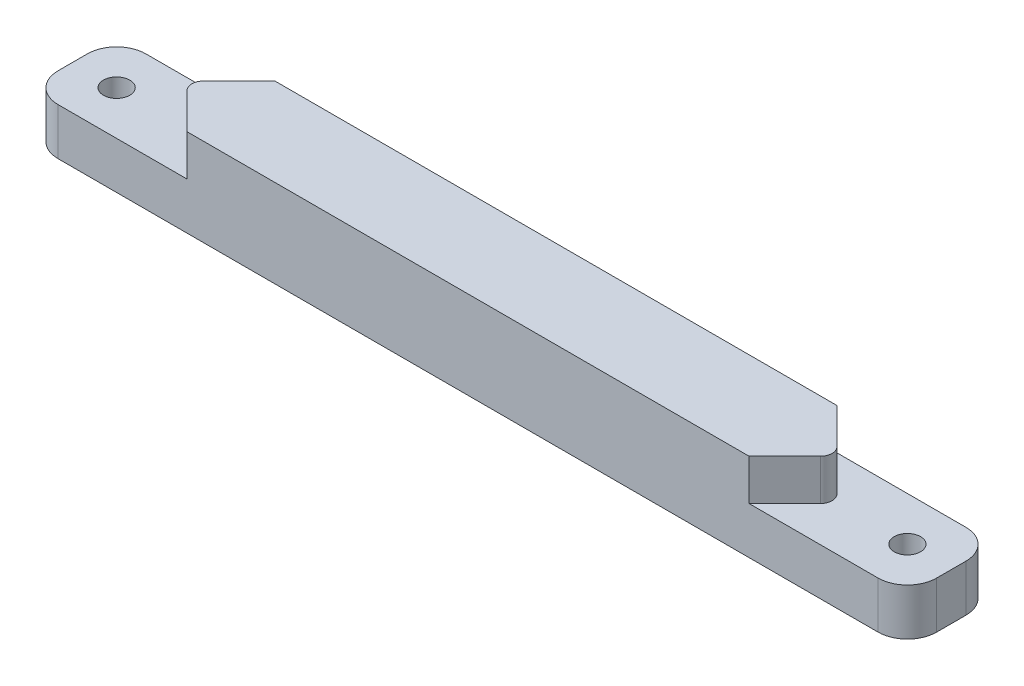
SolidWorks part; units mm, degrees
ref_plane "Front Plane" through (0, 0, 0) normal (0, 0, 1) x (1, 0, 0)
ref_plane "Top Plane" through (0, 0, 0) normal (0, 1, 0) x (1, 0, 0)
ref_plane "Right Plane" through (0, 0, 0) normal (1, 0, 0) x (0, 0, -1)
sketch "Sketch1" plane through (0, 0, 0) normal (0, 1, 0) x (1, 0, 0)
  line L1 (0, 0) -> (150, 0)
  line L2 (0, 0) -> (0, 15)
  line L3 (0, 15) -> (150, 15)
  line L4 (150, 0) -> (150, 15)
  dimension "D1" = 15
  dimension "D2" = 150
extrude "Boss-Extrude1" add sketch "Sketch1" along normal blind 15
ref_plane "Plane1" through (75, 0, 0) normal (1, 0, 0) x (0, 0, -1)
sketch "Sketch2" plane through (0, 15, 0) normal (0, 1, 0) x (1, 0, 0)
  line L0 (0, 0) -> (150, 0) construction
  line L6 (0, 15) -> (16, 15)
  line L7 (0, 15) -> (0, 0)
  line L8 (0, 0) -> (16, 0)
  line L9 (16, 15) -> (16, 0)
  dimension "D2" = 16
extrude "Cut-Extrude1" cut sketch "Sketch2" against normal blind 7
sketch "Sketch3" plane through (0, 8, 0) normal (0, 1, 0) x (1, 0, 0)
  line L3 (16, 0) -> (1, 0)
  line L4 (0, 15) -> (0, 0)
  line L5 (16, 15) -> (0, 15)
  line L6 (0, 15) -> (0, 0)
  line L7 (0, 0) -> (16, 0)
  line L11 (0, 0) -> (16, 0)
  line L16 (16, 0) -> (16, 15)
  circle A0 centre (7.5, 7.5) radius 2.25
  dimension "D2" = 4.5
  dimension "D3" = 7.5
  dimension "D4" = 7.5
  dimension "D1" = 0
extrude "Cut-Extrude2" cut sketch "Sketch3" against normal up to surface (8 mm away) contours A0 up to face at (75, 0, -7.5)
mirror "Mirror1" about plane through (75, 0, 0) normal (1, 0, 0) of "Cut-Extrude2", "Cut-Extrude1"
fillet "Fillet1" radius 5 4 edges at (150, 4, -15) (150, 4, 0) (0, 4, -15) (0, 4, 0)
ref_plane "Plane2" through (0, 0, -7.5) normal (0, 0, 1) x (1, 0, 0)
sketch "Sketch4" plane through (0, 15, 0) normal (0, 1, 0) x (1, 0, 0)
  line L2 (15, 10) -> (15, -130) construction
  line L5 (15, 10) -> (15, -130)
  line L6 (16, 11.0208) -> (27.0208, 0)
  line L7 (27.0208, 0) -> (27.0208, 15) construction
  line L9 (134, 0) -> (134, 15)
  line L15 (134, 15) -> (16, 15)
  line L16 (16, 15) -> (16, 0)
  line L17 (16, 0) -> (134, 0)
  line L19 (27.0208, 15) -> (16, 15)
  line L20 (16, 15) -> (16, 0)
  line L21 (16, 0) -> (27.0208, 0)
  line L22 (27.0208, 15) -> (19.5208, 7.5)
  line M6 (16, 0) -> (134, 0)
  line M8 (134, 15) -> (16, 15)
  line M26 (16, 15) -> (16, 0)
  dimension "D1" = 0
extrude "Cut-Extrude3" cut sketch "Sketch4" against normal up to surface (7 mm away) contours L6 M26 M6 | L22 L6 M8 M26 up to face at (142.5, 8, -5.25)
fillet "Fillet2" radius 2 1 edges at (19.5208, 11.5, -7.5)
mirror "Mirror2" about plane through (75, 0, 0) normal (1, 0, 0) of "Fillet2", "Cut-Extrude3"
